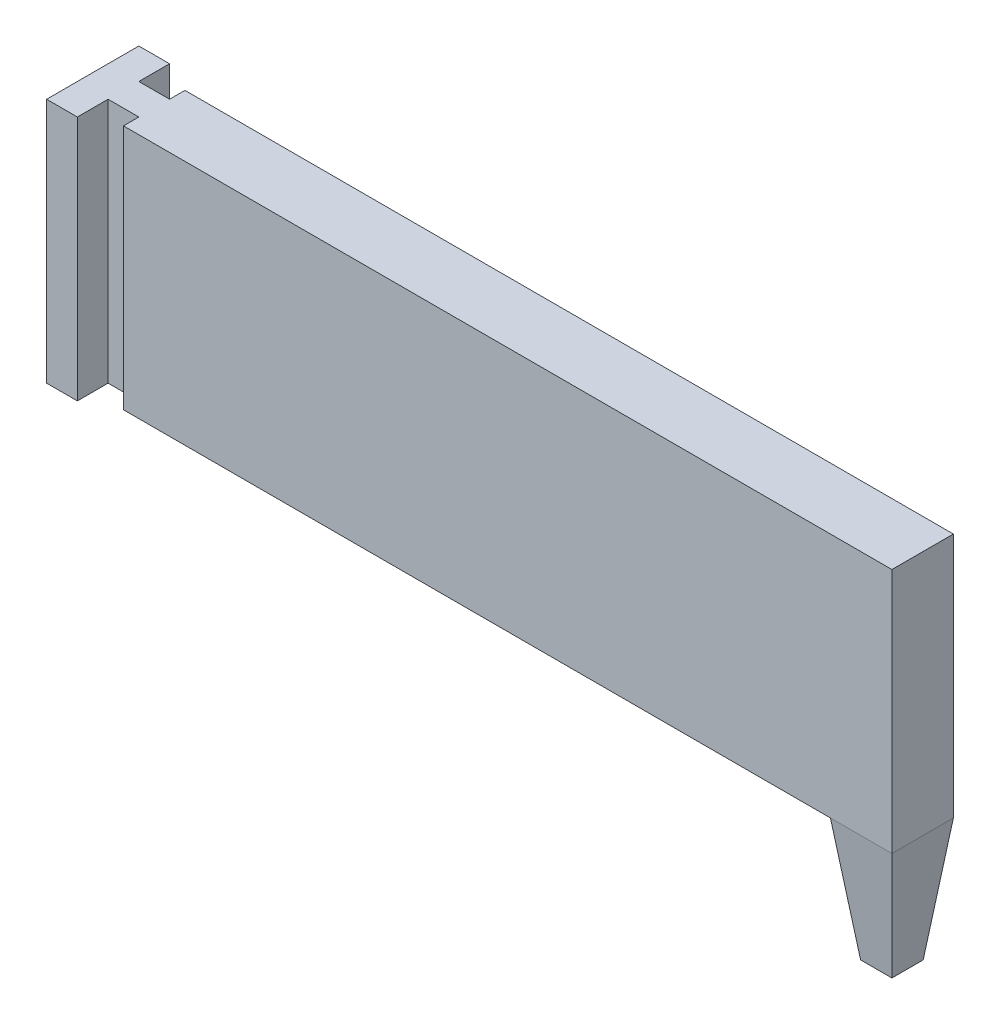
SolidWorks part; units mm, degrees
ref_plane "Front Plane" through (0, 0, 0) normal (0, 0, 1) x (1, 0, 0)
ref_plane "Top Plane" through (0, 0, 0) normal (0, 1, 0) x (1, 0, 0)
ref_plane "Right Plane" through (0, 0, 0) normal (1, 0, 0) x (0, 0, -1)
sketch "Sketch2" plane through (0, 0, 0) normal (0, 1, 0) x (1, 0, 0)
  line L0 (-10, 7.5) -> (-10, -7.5)
  line L1 (-10, -7.5) -> (-5, -7.5)
  line L2 (-5, -7.5) -> (-5, -2.5)
  line L3 (-5, -2.5) -> (0, -2.5)
  line L4 (0, -2.5) -> (0, 2.5)
  line L5 (0, 2.5) -> (-5, 2.5)
  line L6 (-5, 2.5) -> (-5, 7.5)
  line L7 (-5, 7.5) -> (-10, 7.5)
  point P2 (0, 0)
  dimension "D1" = 5
extrude "Boss-Extrude1" add sketch "Sketch2" along normal blind 40
sketch "Sketch3" plane through (0, 0, 0) normal (0, 0, 1) x (1, 0, 0)
  line L0 (0, 0) -> (125, 0)
  line L3 (125, 0) -> (125, 40)
  line L4 (125, 40) -> (0, 40)
  line L6 (0, 40) -> (0, 0)
  point P4 (90.5311, 0)
  point P10 (100, 0)
  point P11 (0, 0)
  point P12 (100, 0)
  point P13 (100, 0.7617)
  dimension "D4" = 125
extrude "Boss-Extrude2" add sketch "Sketch3" along normal blind 5 and the other way blind 5
sketch "Sketch4" plane through (0, 0, 0) normal (0, -1, 0) x (1, 0, 0)
  line L0 (0, 5) -> (125, 5) construction
  line L1 (125, -5) -> (115, -5)
  line L2 (125, -5) -> (125, 5)
  line L3 (125, 5) -> (115, 5)
  line L4 (115, -5) -> (115, 5)
extrude "Boss-Extrude3" add sketch "Sketch4" along normal blind 20 draft 7
